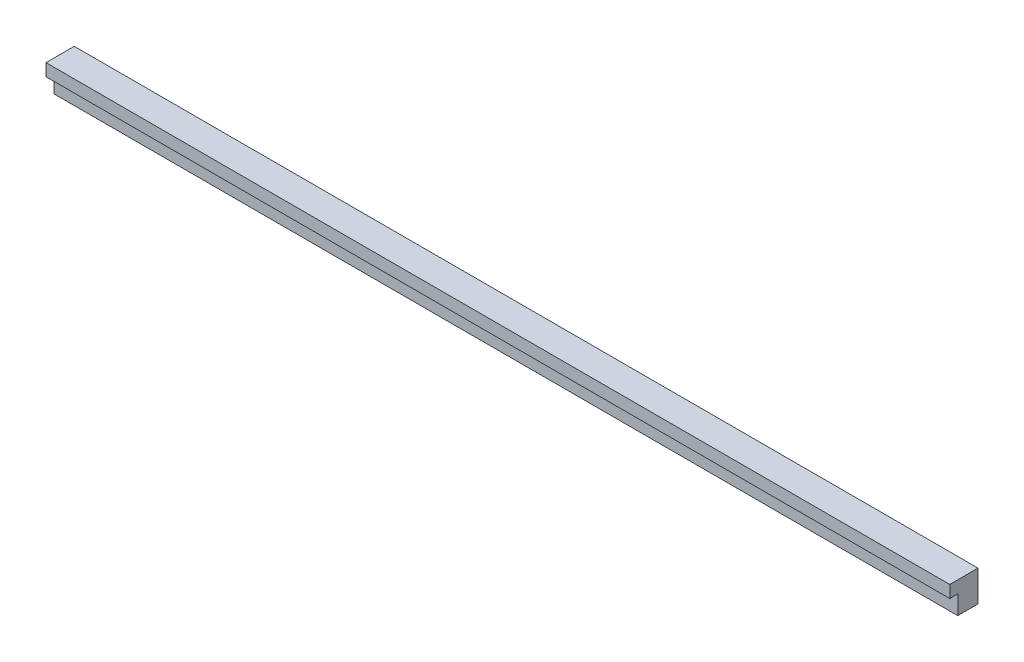
SolidWorks part; units mm, degrees
ref_plane "Plan de face" through (0, 0, 0) normal (0, 0, 1) x (1, 0, 0)
ref_plane "Plan de dessus" through (0, 0, 0) normal (0, 1, 0) x (1, 0, 0)
ref_plane "Plan de droite" through (0, 0, 0) normal (1, 0, 0) x (0, 0, -1)
sketch "Esquisse1" plane through (0, 0, 0) normal (0, 0, 1) x (1, 0, 0)
  line L0 (-319, 181) -> (-319, -181) construction
  line L1 (-319, 195) -> (641, 195)
  line L2 (-319, 195) -> (-319, 162)
  line L3 (-319, 162) -> (641, 162)
  line L4 (641, 195) -> (641, 162)
  line L5 (-199, 181) -> (-319, 181) construction
  line L6 (641, 261) -> (641, -201) construction
  line L8 (-118, 162) -> (-140, 162) construction
  dimension "D2" = 14
extrude "Boss.-Extru.1" add sketch "Esquisse1" along normal up to surface (21.5 mm away) contours L1 L4 L3 L2
sketch "Esquisse2" plane through (0, 0, 21.5) normal (0, 0, 1) x (1, 0, 0)
  line L0 (-319, 162) -> (-319, 195) construction
  line L1 (641, 195) -> (-319, 195)
  line L2 (641, 195) -> (641, 182)
  line L3 (641, 182) -> (-319, 182)
  line L4 (-319, 195) -> (-319, 182)
  line L5 (-199, 181) -> (-319, 181) construction
  dimension "D1" = 1
extrude "Boss.-Extru.2" add sketch "Esquisse2" along normal up to surface (8.5 mm away)
